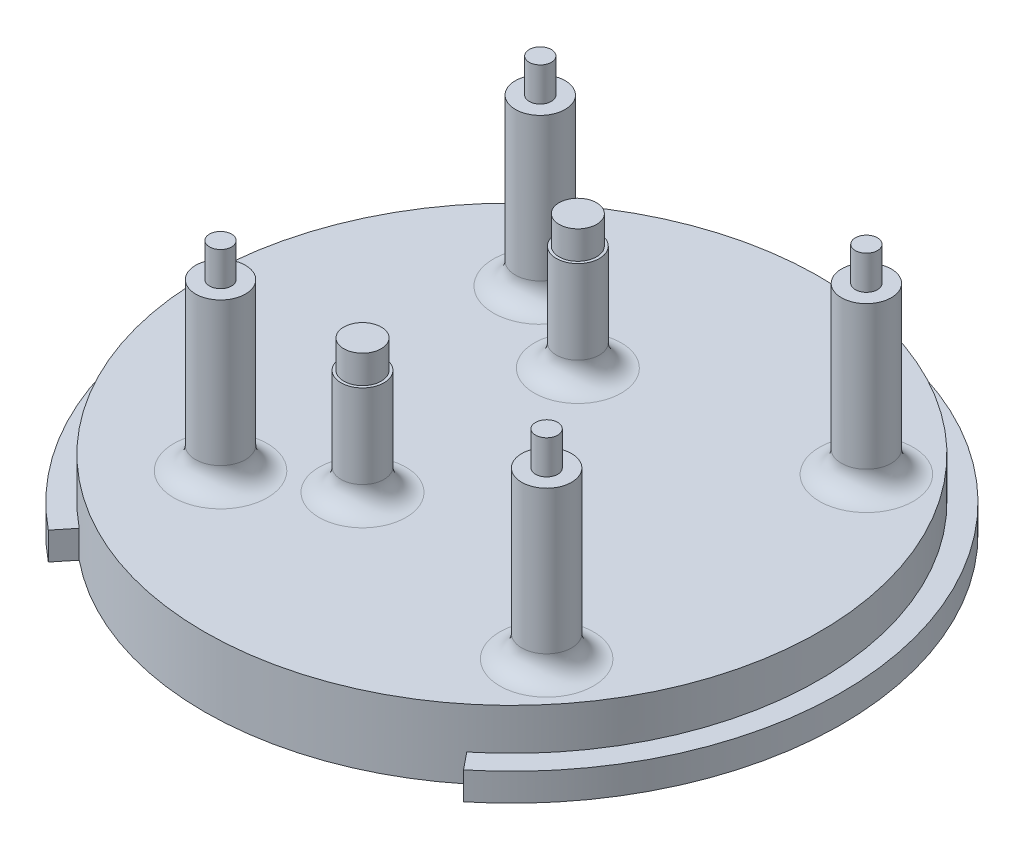
SolidWorks part; units mm, degrees
ref_plane "Front Plane" through (0, 0, 0) normal (0, 0, 1) x (1, 0, 0)
ref_plane "Top Plane" through (0, 0, 0) normal (0, 1, 0) x (1, 0, 0)
ref_plane "Right Plane" through (0, 0, 0) normal (1, 0, 0) x (0, 0, -1)
sketch "Sketch1" plane through (0, 0, 0) normal (0, 1, 0) x (1, 0, 0)
  circle A0 centre (0, 0) radius 23.8125
  dimension "D1" = 47.625
extrude "Boss-Extrude1" add sketch "Sketch1" along normal blind 2
sketch "Sketch2" plane through (0, 2, 0) normal (0, 1, 0) x (1, 0, 0)
  circle A0 centre (0, 0) radius 22.225
  dimension "D1" = 44.45
extrude "Boss-Extrude2" add sketch "Sketch2" along normal blind 3
sketch "Sketch4" plane through (0, 2, 0) normal (0, 1, 0) x (1, 0, 0)
  line L0 (-15, -18.4942) -> (15, -18.4942) construction
  line L1 (-15, -18.4942) -> (-14, -17.2612)
  line L2 (15, -18.4942) -> (14, -17.2612)
  line L3 (15, -18.4942) -> (16.769, -17.0594) construction
  line L4 (-15, -18.4942) -> (-17.0723, -16.8134) construction
  circle A0 centre (0, 0) radius 23.8125 construction
  arc A1 (-15, -18.4942) -> (15, -18.4942) centre (0, 0) ccw
  circle A2 centre (0, 0) radius 22.225 construction
  arc A3 (-14, -17.2612) -> (14, -17.2612) centre (0, 0) ccw
  dimension "D1" = 30
extrude "Cut-Extrude2" cut sketch "Sketch4" against normal through all
sketch "Sketch6" plane through (0, 5, 0) normal (0, 1, 0) x (1, 0, 0)
  circle A0 centre (-9.5, 11.55) radius 1.8
  circle A1 centre (-9.5, -11.55) radius 1.8
  circle A2 centre (14.06, -11.55) radius 1.8
  circle A3 centre (14.06, 11.55) radius 1.8
extrude "Boss-Extrude3" add sketch "Sketch6" along normal up to surface (11.95 mm away)
sketch "Sketch7" plane through (0, 5, 0) normal (0, 1, 0) x (1, 0, 0)
  circle A0 centre (-3.0148, -7.7787) radius 1.5558
  circle A1 centre (-3.0148, 7.7788) radius 1.5557
extrude "Boss-Extrude4" add sketch "Sketch7" along normal up to surface (7.632 mm away)
sketch "Sketch8" plane through (0, 16.95, 0) normal (0, 1, 0) x (1, 0, 0)
  circle A2 centre (-9.5, 11.55) radius 0.8
  circle A3 centre (-9.5, 11.55) radius 0.8
  circle A5 centre (-9.5, -11.55) radius 0.8
  circle A6 centre (-9.5, -11.55) radius 0.8
  circle A15 centre (14.06, -11.55) radius 0.8
  circle A16 centre (14.06, -11.55) radius 0.8
  circle A18 centre (14.06, 11.55) radius 0.8
  circle A19 centre (14.06, 11.55) radius 0.8
  dimension "D1" = 0.2
  dimension "D2" = 0.2
  dimension "D3" = 0.2
  dimension "D4" = 0.2
extrude "Boss-Extrude5" add sketch "Sketch8" along normal up to surface (2.45 mm away)
sketch "Sketch9" plane through (0, 12.632, 0) normal (0, 1, 0) x (1, 0, 0)
  circle A2 centre (-3.0148, 7.7788) radius 1.3557
  circle A3 centre (-3.0148, 7.7788) radius 1.3557
  circle A5 centre (-3.0148, -7.7787) radius 1.3557
  circle A6 centre (-3.0148, -7.7787) radius 1.3557
  dimension "D1" = 0.2
  dimension "D2" = 0.2
extrude "Boss-Extrude6" add sketch "Sketch9" along normal up to surface (2.032 mm away)
fillet "Fillet1" radius 1.5875 6 edges at (14.06, 5, -9.75) (14.06, 5, 13.35) (-3.0148, 5, 9.3345) (-3.0148, 5, -6.223) (-9.5, 5, -9.75) (-9.5, 5, 13.35)
